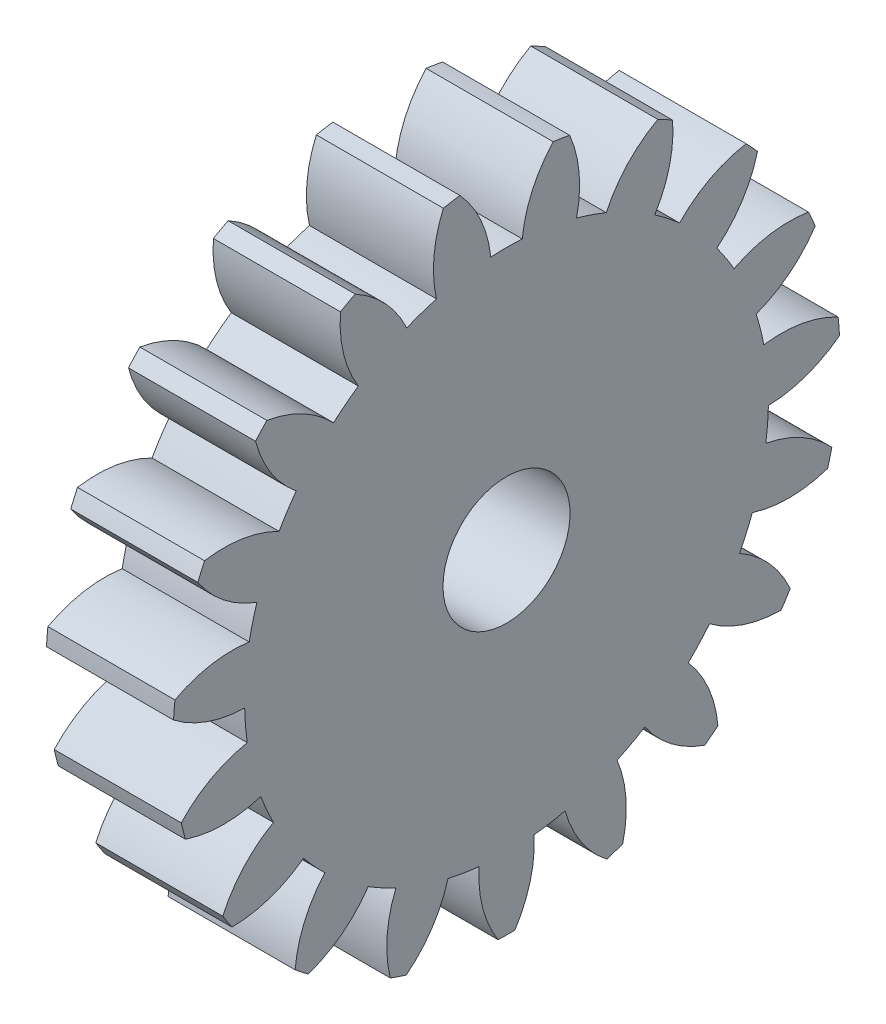
SolidWorks part; units mm, degrees
ref_plane "Plane1" through (0, 0, 0) normal (0, 0, 1) x (1, 0, 0)
ref_plane "Plane2" through (0, 0, 0) normal (0, 1, 0) x (1, 0, 0)
ref_plane "Plane3" through (0, 0, 0) normal (1, 0, 0) x (0, 0, -1)
sketch "HoldingSke" plane through (0, 0, 0) normal (0, 1, 0) x (1, 0, 0)
  line L0 (0, 0) -> (3.7821, -1.3023)
  line L1 (-15, 0) -> (100, 0) construction
  line L2 (0, 0) -> (-2.1039, 2.3779)
  line L3 (0, 0) -> (-11.863, 4.5341)
  line L4 (0, 0) -> (8.1655, 2.8116)
  line L5 (0, 0) -> (-46.8476, -17.4728)
  line L6 (0, 0) -> (-0.829, -0.5593)
  line L7 (-2.1039, 2.3779) -> (8.6586, 51.2059)
  line L8 (-76.2, 54.61) -> (-76.1, 54.61)
  line L9 (-71.009, 38.7566) -> (-53.1078, 45.2721)
  line L10 (-76.2, 71.12) -> (104.1128, 71.12)
  line L11 (0, 0) -> (-1, 0)
  line L12 (-76.2, 101.6) -> (-76.192, 101.6)
  line L13 (24.9733, 27.94) -> (52.9518, 28.4284)
  line L14 (24.9733, 27.94) -> (24.9743, 27.94)
  line L15 (24.9733, 27.94) -> (100.4006, 29.5858)
  line L16 (-63.627, -0.25) -> (-12.827, -0.25)
  circle A0 centre (0, 0) radius 0.5
  circle A1 centre (0, 0) radius 2.0615
  circle A2 centre (0, 0) radius 37.5
  circle A3 centre (0, 0) radius 0.5
  dimension "MHD" = 4.123
  dimension "Hub_dia" = 75
  dimension "Bore" = 1
  dimension "MBD" = 1
  dimension "Num_teeth" = 19
  dimension "Pitch" = 4
  dimension "Overall_len" = 50
  dimension "Show_teeth" = 19
  dimension "Thickness" = 1
  dimension "OAL" = 50.0001
  dimension "T_dim" = 0.1
  dimension "Ap" = 20
  dimension "H" = 19.05
  dimension "Pitch_radius" = 180.3128
  dimension "Width" = 1
  dimension "Backlash" = 0.008
  dimension "Addendum_fac" = 1
  dimension "Dedendum_fac" = 1.25
  dimension "Clearance_fac" = 0.25
  dimension "Dedendum_add" = 0.001
  dimension "Module" = 0.25
sketch "BasProSke" plane through (0, 0, 0) normal (0, 1, 0) x (1, 0, 0)
  line L0 (-10, 0) -> (60, 0) construction
  line L1 (0, 0) -> (0, 2.625)
  line L2 (0, 0) -> (1, 0)
  line L3 (1, 0) -> (1, 2.625)
  line L4 (1, 2.625) -> (0, 2.625)
  dimension "Thickness" = 1
  dimension "Diameter" = 5.25
revolve "Base-Revolve" add sketch "BasProSke" angle 360 about L0
sketch "TooCutSke" plane through (0, 0, 0) normal (1, 0, 0) x (0, 0, -1)
  line L1 (0, 0) -> (0, 107) construction
  line L2 (0, 0) -> (-0.2101, 2.3657) construction
  line L3 (0, 0) -> (-0.7795, 4.6714) construction
  line L4 (-0.2101, 2.3657) -> (-0.3898, 2.3357) construction
  arc A0 (0.1239, 2.0578) -> (-0.1239, 2.0578) centre (0, 0) ccw
  arc A1 (0.388, 2.6218) -> (-0.388, 2.6218) centre (0, 0) ccw
  circle A2 centre (0, 0) radius 2.375 construction
  circle A3 centre (0, 0) radius 2.2318 construction
  arc A4 (-0.1239, 2.0578) -> (-0.388, 2.6218) centre (-1.0688, 1.9592) ccw
  arc A5 (0.388, 2.6218) -> (0.1239, 2.0578) centre (1.0688, 1.9592) ccw
  dimension "Root_dia" = 4.123
  dimension "Overcut_dia" = 5.3008
  dimension "Pitch_dia" = 4.75
  dimension "Base_dia" = 4.4635
  dimension "Flank_rad" = 0.95
  dimension "Half_ang" = 9.474
  dimension "Half_CT" = 0.1821
extrude "ToothCut" cut sketch "TooCutSke" along normal through all
fillet "Breaks" [suppressed] radius 0.005
fillet "RootFillets" [suppressed] radius 0.0635
pattern_circular "TeethCuts" count 19 every 18.947 about axis through (-10, 0, 0) along (1, 0, 0) of "ToothCut", "RootFillets", "Breaks"
sketch "HubNeaOneSke" plane through (0, 0, 0) normal (-1, 0, 0) x (0, 0, 1)
  circle A0 centre (0, 0) radius 2.0615
  dimension "Diameter" = 4.123
extrude "HubNearOne" [suppressed] add sketch "HubNeaOneSke" along normal blind 49.0001
sketch "HubNeaBotSke" plane through (0, 0, 0) normal (-1, 0, 0) x (0, 0, 1)
  circle A0 centre (0, 0) radius 2.0615
  dimension "Diameter" = 4.123
extrude "HubNearBoth" [suppressed] add sketch "HubNeaBotSke" along normal blind 24.5
ref_plane "FarPln" through (1, 0, 0) normal (1, 0, 0) x (0, 0, -1)
sketch "HubFarSke" plane through (1, 0, 0) normal (1, 0, 0) x (0, 0, -1)
  circle A0 centre (0, 0) radius 2.0615
  dimension "Diameter" = 4.123
extrude "HubFar" [suppressed] add sketch "HubFarSke" along normal blind 24.5
sketch "BorSke" plane through (0, 0, 0) normal (1, 0, 0) x (0, 0, -1)
  circle A0 centre (0, 0) radius 0.5
  dimension "Diameter" = 1
extrude "Bore" cut sketch "BorSke" along normal mid plane 100.0001
sketch "KeySke" plane through (0, 0, 0) normal (1, 0, 0) x (0, 0, -1)
  line L0 (-0.05, 0) -> (-0.05, 0.6)
  line L1 (-0.05, 0.6) -> (0.05, 0.6)
  line L2 (0.05, 0.6) -> (0.05, 0)
  line L3 (0, 0) -> (0, 34) construction
  line L4 (-0.05, 0) -> (0.05, 0)
  dimension "Offset" = 0.6
extrude "Keyway" [suppressed] cut sketch "KeySke" along normal mid plane 100.0001
pattern_circular "Keyway2" [suppressed] count 2 every 90 about axis through (-10, 0, 0) along (1, 0, 0)
equation "' \"Module@HoldingSke\" = 6.35"
equation "' \"Num_teeth@HoldingSke\" = 12"
equation "' \"Ap@HoldingSke\" =  20"
equation "' \"Ap@HoldingSke\" = 20"
equation "' \"Width@HoldingSke\" = 0.5 * 25.4"
equation "' \"Hub_dia@HoldingSke\"= 1 * 25.4"
equation "' \"Hub_dia@HoldingSke\" = 1 * 25.4"
equation "' \"Overall_len@HoldingSke\" = 1.0 * 25.4"
equation "' \"Bore@HoldingSke\" = 0.75 * 25.4"
equation "' \"T_dim@HoldingSke\" = 0.1 * 25.4"
equation "' \"Width@KeySke\" = 0.25 * 25.4"
equation "' \"Show_teeth@HoldingSke\" = 13"
equation "' \"Backlash@HoldingSke\" = 0.009 * 25.4"
equation "' \"Addendum_fac@HoldingSke\" = 1.0"
equation "' \"Dedendum_fac@HoldingSke\" = 1.25"
equation "' \"Dedendum_add@HoldingSke\" = 0.00005 * 25.4"
equation "' \"Clearance_fac@HoldingSke\" = 0.25"
equation "\"Pitch@HoldingSke\" = 1 / \"Module@HoldingSke\""
equation "\"Overcut_dia@TooCutSke\" = (\"Num_teeth@HoldingSke\" + 2 * \"Addendum_fac@HoldingSke\") / \"Pitch@HoldingSke\" + 0.002 * 25.4"
equation "\"Pitch_dia@TooCutSke\" = \"Num_teeth@HoldingSke\" / \"Pitch@HoldingSke\""
equation "\"Base_dia@TooCutSke\" = \"Num_teeth@HoldingSke\" / \"Pitch@HoldingSke\" * cos((\"Ap@HoldingSke\"  * 3.14159265 / 180))"
equation "\"Root_dia@TooCutSke\" = (\"Num_teeth@HoldingSke\" + 2) / \"Pitch@HoldingSke\" - 2 * (\"Addendum_fac@HoldingSke\" + \"Dedendum_fac@HoldingSke\") / \"Pitch@HoldingSke\" - \"Dedendum_add@HoldingSke\" * 2"
equation "\"Half_ang@TooCutSke\" = 180 / \"Num_teeth@HoldingSke\""
equation "\"Half_CT@TooCutSke\" = \"Num_teeth@HoldingSke\" / \"Pitch@HoldingSke\" * sin((3.14159265 / 2 / \"Num_teeth@HoldingSke\")) / 2 - 7 * \"Backlash@HoldingSke\" / 4"
equation "\"Flank_rad@TooCutSke\" = \"Num_teeth@HoldingSke\" / \"Pitch@HoldingSke\" / 5"
equation "\"Radius@RootFillets\" = \"Clearance_fac@HoldingSke\" / \"Pitch@HoldingSke\" + \"Dedendum_add@HoldingSke\""
equation "\"Break_rad@Breaks\" = 0.02 / \"Pitch@HoldingSke\""
equation "\"Thickness@HoldingSke\" = \"Width@HoldingSke\""
equation "\"OAL@HoldingSke\" = \"Thickness@HoldingSke\""
equation "\"MHD@HoldingSke\" = (\"Num_teeth@HoldingSke\" + 2) / \"Pitch@HoldingSke\" - 2 * (\"Addendum_fac@HoldingSke\" + \"Dedendum_fac@HoldingSke\")  / \"Pitch@HoldingSke\" - \"Dedendum_add@HoldingSke\" * 2"
equation "\"MBD@HoldingSke\" = (\"Num_teeth@HoldingSke\" + 2) / \"Pitch@HoldingSke\" - 2 * (\"Addendum_fac@HoldingSke\" + \"Dedendum_fac@HoldingSke\")  / \"Pitch@HoldingSke\" - \"Dedendum_add@HoldingSke\" * 2 - 0.002 * 25.4"
equation "\"MHD@HoldingSke\" = ((sgn( \"MHD@HoldingSke\" - \"Hub_dia@HoldingSke\" )-1)*( \"MHD@HoldingSke\" - \"Hub_dia@HoldingSke\" ))/-2+ \"Hub_dia@HoldingSke\""
equation "\"MBD@HoldingSke\" = ((sgn( \"MBD@HoldingSke\" - \"Bore@HoldingSke\" )-1)*( \"MBD@HoldingSke\" - \"Bore@HoldingSke\" ))/-2+ \"Bore@HoldingSke\""
equation "\"OAL@HoldingSke\" = ((sgn( \"OAL@HoldingSke\" - \"Overall_len@HoldingSke\" )+1)*( \"OAL@HoldingSke\" - \"Overall_len@HoldingSke\" ))/2 + \"Overall_len@HoldingSke\" + 0.000002 * 25.4"
equation "\"Num_teeth@TeethCuts\" = int( \"Show_teeth@HoldingSke\" ) + 1"
equation "\"Num_teeth@TeethCuts\" = ((sgn( \"Num_teeth@TeethCuts\" - \"Num_teeth@HoldingSke\" )-1)*( \"Num_teeth@TeethCuts\" - \"Num_teeth@HoldingSke\" ))/-2+ \"Num_teeth@HoldingSke\""
equation "\"Num_teeth@TeethCuts\" = ((sgn( \"Num_teeth@TeethCuts\" - 2.0)+1)*( \"Num_teeth@TeethCuts\" - 2.0))/2 +2.0"
equation "\"Angle@TeethCuts\" = 360.0 / \"Num_teeth@HoldingSke\""
equation "\"Diameter@BasProSke\" = (\"Num_teeth@HoldingSke\" + 2 * \"Addendum_fac@HoldingSke\") / \"Pitch@HoldingSke\""
equation "\"Thickness@BasProSke\"  = \"Thickness@HoldingSke\""
equation "' \"Fillet_rad@BasProSke\" =  \"Thickness@HoldingSke\" * 0.05"
equation "' \"Fillet_rad@BasProSke\" = \"Thickness@HoldingSke\" * 0.05"
equation "\"MHD@HoldingSke\" = ((sgn( \"MHD@HoldingSke\" - \"Root_dia@TooCutSke\" )-1)*( \"MHD@HoldingSke\" - \"Root_dia@TooCutSke\" ))/-2+ \"Root_dia@TooCutSke\""
equation "\"Diameter@HubNeaOneSke\" = \"MHD@HoldingSke\""
equation "\"Length@HubNearOne\" = \"OAL@HoldingSke\" - \"Thickness@BasProSke\""
equation "\"Diameter@HubNeaBotSke\" = \"MHD@HoldingSke\""
equation "\"Length@HubNearBoth\" = ( \"OAL@HoldingSke\" - \"Thickness@BasProSke\" ) / 2.0"
equation "\"Thickness@FarPln\" = \"Thickness@BasProSke\""
equation "\"Diameter@HubFarSke\" = \"MHD@HoldingSke\""
equation "\"Length@HubFar\" = ( \"OAL@HoldingSke\" - \"Thickness@BasProSke\" ) / 2.0"
equation "\"Diameter@BorSke\" = \"MBD@HoldingSke\""
equation "\"D1@Bore\" = \"OAL@HoldingSke\" * 2.0"
equation "\"D1@Keyway\" = \"OAL@HoldingSke\" * 2.0"
equation "\"Offset@KeySke\" = \"T_dim@HoldingSke\" + \"MBD@HoldingSke\" / 2.0"
